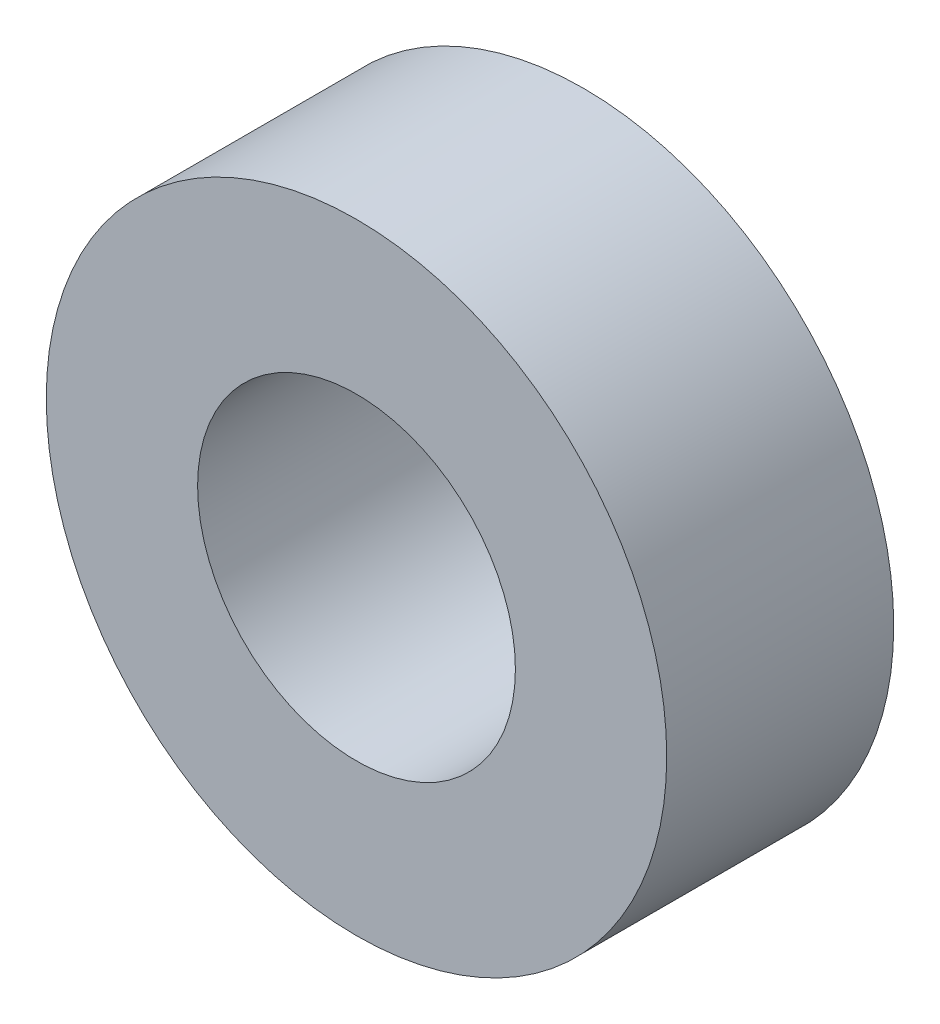
SolidWorks part; units mm, degrees
ref_plane "Plan de face" through (0, 0, 0) normal (0, 0, 1) x (1, 0, 0)
ref_plane "Plan de dessus" through (0, 0, 0) normal (0, 1, 0) x (1, 0, 0)
ref_plane "Plan de droite" through (0, 0, 0) normal (1, 0, 0) x (0, 0, -1)
sketch "Esquisse1" plane through (0, 0, 0) normal (0, 0, 1) x (1, 0, 0)
  circle A0 centre (0, 0) radius 1.05
  dimension "D1" = 2.1
extrude "Extru.-Mince1" add sketch "Esquisse1" along normal blind 1.5 thin
